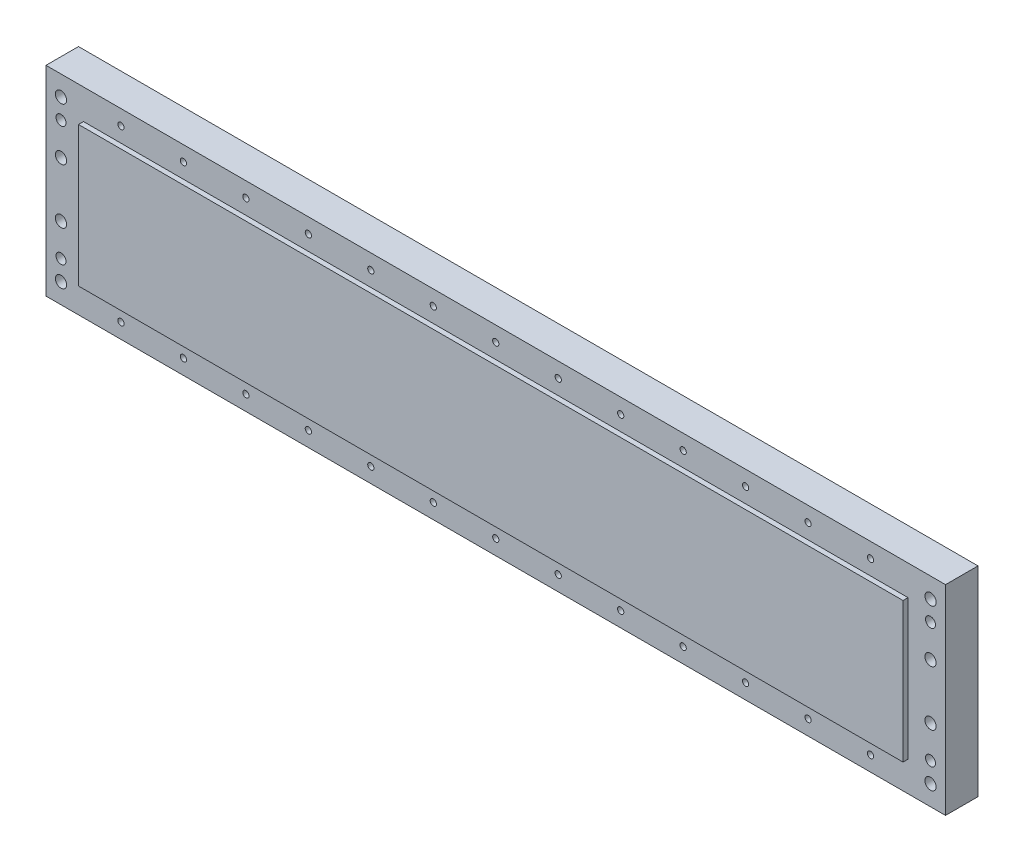
SolidWorks part; units mm, degrees
ref_plane "Alzado" through (0, 0, 0) normal (0, 0, 1) x (1, 0, 0)
ref_plane "Planta" through (0, 0, 0) normal (0, 1, 0) x (1, 0, 0)
ref_plane "Vista lateral" through (0, 0, 0) normal (1, 0, 0) x (0, 0, -1)
sketch "Croquis1" plane through (0, 0, 0) normal (0, 0, 1) x (1, 0, 0)
  line L1 (360, 80) -> (0, 80)
  line L2 (360, 80) -> (360, 0)
  line L3 (360, 0) -> (0, 0)
  line L4 (0, 80) -> (0, 0)
  dimension "D1" = 80
  dimension "D2" = 360
extrude "Saliente-Extruir1" add sketch "Croquis1" along normal blind 15
sketch "Croquis2" plane through (0, 0, 15) normal (0, 0, 1) x (1, 0, 0)
  line L0 (360, 80) -> (360, 0)
  line L1 (0, 80) -> (360, 80)
  line L3 (15, 68) -> (345, 68)
  line L5 (0, 0) -> (360, 0)
  line L7 (15, 12) -> (345, 12)
  line L9 (360, 0) -> (360, 80) construction
  line L11 (360, 80) -> (0, 80) construction
  line L15 (345, 68) -> (345, 12)
  line L16 (0, 80) -> (0, 0)
  line L17 (15, 68) -> (15, 12)
  dimension "D3" = 12
  dimension "D1" = 15
  dimension "D2" = 15
  dimension "D8" = 12
extrude "Cortar-Extruir1" cut sketch "Croquis2" against normal blind 2
hole_wizard "Taladro roscado M31" positions "Croquis3" profile "Croquis4" tap size "M3" standard "DIN"
sketch "Croquis3" plane through (0, 0, 13) normal (0, 0, 1) x (1, 0, 0)
  line L0 (0, 68) -> (0, 12) construction
  line L1 (0, 0) -> (360, 0) construction
  point P0 (30, 6)
  dimension "D1" = 30
  dimension "D2" = 6
cosmetic thread "Rosca de taladro1" parameters "D1"=6, "D2"=3
sketch "Croquis4" plane through (30, 6, 13) normal (1, 0, 0) x (0, -1, 0)
  line L0 (0, 0) -> (0, 7.7511)
  line L1 (0, 7.7511) -> (1.25, 7)
  line L2 (1.25, 7) -> (1.25, 0)
  line L5 (1.25, 0) -> (0, 0)
  line L10 (0, 7.7511) -> (-1.25, 7) construction
  line L11 (0, -6.35) -> (0, 107.95) construction
  dimension "Diámetro de perforador para roscar" = 2.5
  dimension "Profundidad de perforador para roscar" = 7
  dimension "Ángulo de perforador" = 118
hole_wizard "Refrentado para tornillo con cabeza hueca de M41" positions "Croquis5" profile "Croquis6" counterbore size "M4" standard "DIN" end condition through all
sketch "Croquis5" plane through (0, 0, 0) normal (0, 0, -1) x (-1, 0, 0)
  line L1 (-360, 80) -> (0, 80) construction
  line L2 (-354, 80) -> (-354, 0) construction
  line L3 (0, 0) -> (-360, 0) construction
  line L5 (-360, 0) -> (-360, 80) construction
  line L6 (-6, 80) -> (-6, 0) construction
  line L8 (0, 80) -> (0, 0) construction
  point P0 (-6, 72)
  point P2 (-6, 8)
  point P4 (-354, 72)
  point P6 (-354, 8)
  point P17 (-354, 51)
  point P19 (-354, 29)
  point P44 (-6, 51)
  point P46 (-6, 29)
  dimension "D1" = 6
  dimension "D2" = 29
  dimension "D3" = 8
  dimension "D4" = 8
  dimension "D5" = 8
  dimension "D6" = 6
  dimension "D7" = 29
  dimension "D8" = 8
  dimension "D9" = 29
  dimension "D10" = 29
sketch "Croquis6" plane through (6, 72, 0) normal (1, 0, 0) x (0, 1, 0)
  line L0 (0, 0) -> (0, 15)
  line L1 (0, 15) -> (2.25, 15)
  line L3 (2.25, 15) -> (2.25, 4.4)
  line L4 (2.25, 4.4) -> (4, 4.4)
  line L5 (4, 4.4) -> (4, 0)
  line L7 (4, 0) -> (0, 0)
  line L11 (0, -6.35) -> (0, 107.95) construction
  dimension "Diámetro de taladro hasta el siguiente" = 4.5
  dimension "Profundidad de taladro hasta el siguiente" = 15
  dimension "Diámetro de refrentado" = 8
  dimension "Profundidad de refrentado" = 4.4
hole_wizard "Taladros de espiga de Ø4.0mm1" positions "Croquis7" profile "Croquis8" hole size "Ø4.0" standard "DIN" end condition through all
sketch "Croquis7" plane through (0, 0, 0) normal (0, 0, -1) x (-1, 0, 0)
  point P0 (-6, 64)
  point P2 (-6, 16)
  point P4 (-354, 64)
  point P6 (-354, 16)
  dimension "D1" = 16
  dimension "D2" = 16
  dimension "D3" = 6
  dimension "D4" = 6
  dimension "D5" = 16
  dimension "D6" = 6
  dimension "D7" = 6
  dimension "D8" = 16
sketch "Croquis8" plane through (6, 64, 0) normal (1, 0, 0) x (0, 1, 0)
  line L0 (0, 0) -> (0, 15)
  line L1 (0, 15) -> (2, 15)
  line L2 (2, 15) -> (2, 0)
  line L5 (2, 0) -> (0, 0)
  line L11 (0, -6.35) -> (0, 107.95) construction
  dimension "Diámetro de taladro hasta el siguiente" = 4
  dimension "Profundidad de taladro hasta el siguiente" = 15
hole_wizard "Taladro roscado M3x0.351" positions "Croquis9" profile "Croquis10" tap size "M3x0.35" standard "DIN"
sketch "Croquis9" plane through (0, 0, 0) normal (0, 0, -1) x (-1, 0, 0)
  line L0 (0, 0) -> (-360, 0) construction
  line L1 (0, 80) -> (0, 0) construction
  point P0 (-21, 73.5)
  point P2 (-51, 73.5)
  point P4 (-51, 6.5)
  point P6 (-21, 6.5)
  dimension "D1" = 6.5
  dimension "D2" = 6.5
  dimension "D3" = 6.5
  dimension "D4" = 6.5
  dimension "D5" = 21
  dimension "D6" = 51
  dimension "D7" = 21
  dimension "D8" = 51
sketch "Croquis10" plane through (21, 73.5, 0) normal (1, 0, 0) x (0, 1, 0)
  line L0 (0, 0) -> (0, 8.5461)
  line L1 (0, 8.5461) -> (1.325, 7.75)
  line L2 (1.325, 7.75) -> (1.325, 0)
  line L5 (1.325, 0) -> (0, 0)
  line L10 (0, 8.5461) -> (-1.325, 7.75) construction
  line L11 (0, -6.35) -> (0, 107.95) construction
  dimension "Diámetro de perforador para roscar" = 2.65
  dimension "Profundidad de perforador para roscar" = 7.75
  dimension "Ángulo de perforador" = 118
cosmetic thread "Rosca de taladro2" parameters "D1"=6, "D2"=3
cosmetic thread "Rosca de taladro3" parameters "D1"=6, "D2"=3
cosmetic thread "Rosca de taladro4" parameters "D1"=6, "D2"=3
cosmetic thread "Rosca de taladro5" parameters "D1"=6, "D2"=3
pattern_linear "MatrizL1" count 13 spacing 25 along (1, 0, 0) count 2 spacing 68 along (0, 1, 0) of "Taladro roscado M31"
